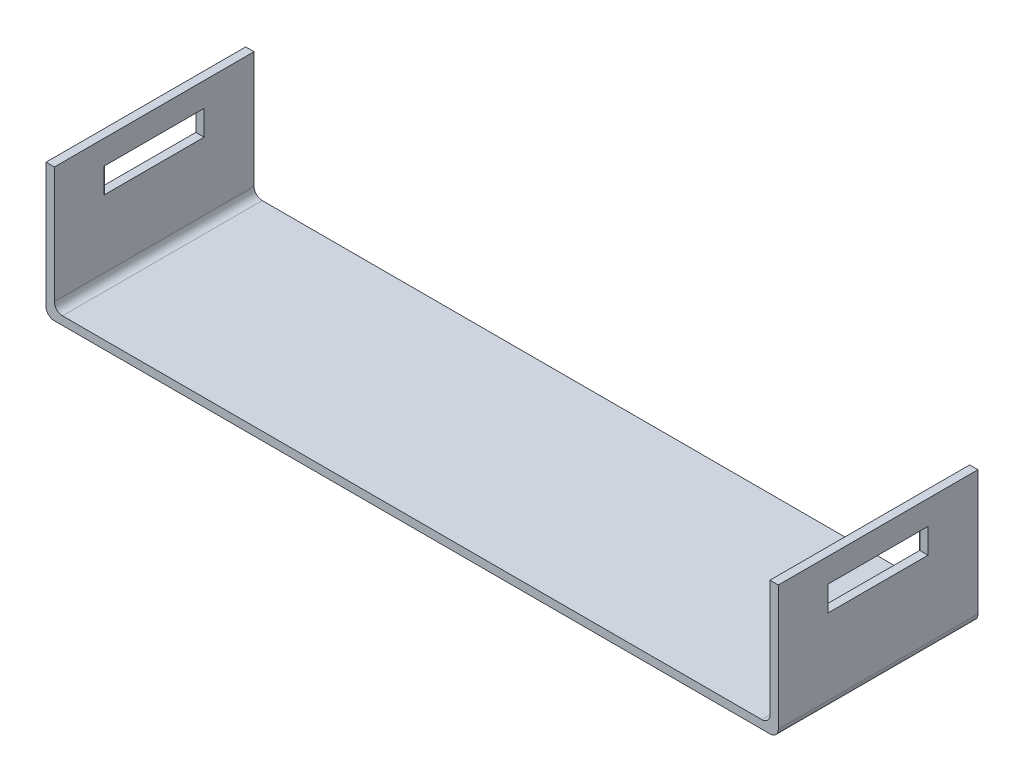
SolidWorks part; units mm, degrees
ref_plane "Front Plane" through (0, 0, 0) normal (0, 0, 1) x (1, 0, 0)
ref_plane "Top Plane" through (0, 0, 0) normal (0, 1, 0) x (1, 0, 0)
ref_plane "Right Plane" through (0, 0, 0) normal (1, 0, 0) x (0, 0, -1)
sketch "Sketch1" plane through (0, 0, 0) normal (0, 0, 1) x (1, 0, 0)
  line L0 (-21.5, 7.5) -> (-21.5, 0.49)
  line L1 (-21.01, 0) -> (0, 0)
  line L2 (0, 0) -> (21.01, 0)
  line L3 (21.5, 0.49) -> (21.5, 7.5)
  line L4 (21.5, 7.5) -> (22, 7.5)
  line L5 (22, 7.5) -> (22, -0.01)
  line L6 (21.51, -0.5) -> (-21.51, -0.5)
  line L7 (-22, -0.01) -> (-22, 7.5)
  line L8 (-22, 7.5) -> (-21.5, 7.5)
  arc A0 (21.01, 0) -> (21.5, 0.49) centre (21.01, 0.49) ccw
  arc A1 (22, -0.01) -> (21.51, -0.5) centre (21.51, -0.01) cw
  arc A2 (-21.51, -0.5) -> (-22, -0.01) centre (-21.51, -0.01) cw
  arc A3 (-21.5, 0.49) -> (-21.01, 0) centre (-21.01, 0.49) ccw
  point P14 (22, -0.5)
  point P17 (-22, -0.5)
  dimension "D5" = 0.49
  dimension "D1" = 0.5
  dimension "D2" = 0.5
  dimension "D3" = 8
  dimension "D4" = 44
extrude "Boss-Extrude1" add sketch "Sketch1" along normal blind 12
sketch "Sketch2" plane through (-22, 0, 0) normal (-1, 0, 0) x (0, 0, 1)
  line L0 (0, 7.5) -> (0, -0.01) construction
  line L1 (3, 6.05) -> (9, 6.05)
  line L2 (3, 6.05) -> (3, 4.55)
  line L3 (3, 4.55) -> (9, 4.55)
  line L4 (9, 6.05) -> (9, 4.55)
  line L5 (3, 6.05) -> (9, 4.55) construction
  line L6 (3, 4.55) -> (9, 6.05) construction
  line L7 (12, 7.5) -> (0, 7.5) construction
  point P0 (6, 5.3)
  dimension "D1" = 6
  dimension "D2" = 2.2
  dimension "D3" = 6
  dimension "D4" = 1.5
extrude "Cut-Extrude1" cut sketch "Sketch2" against normal through all
